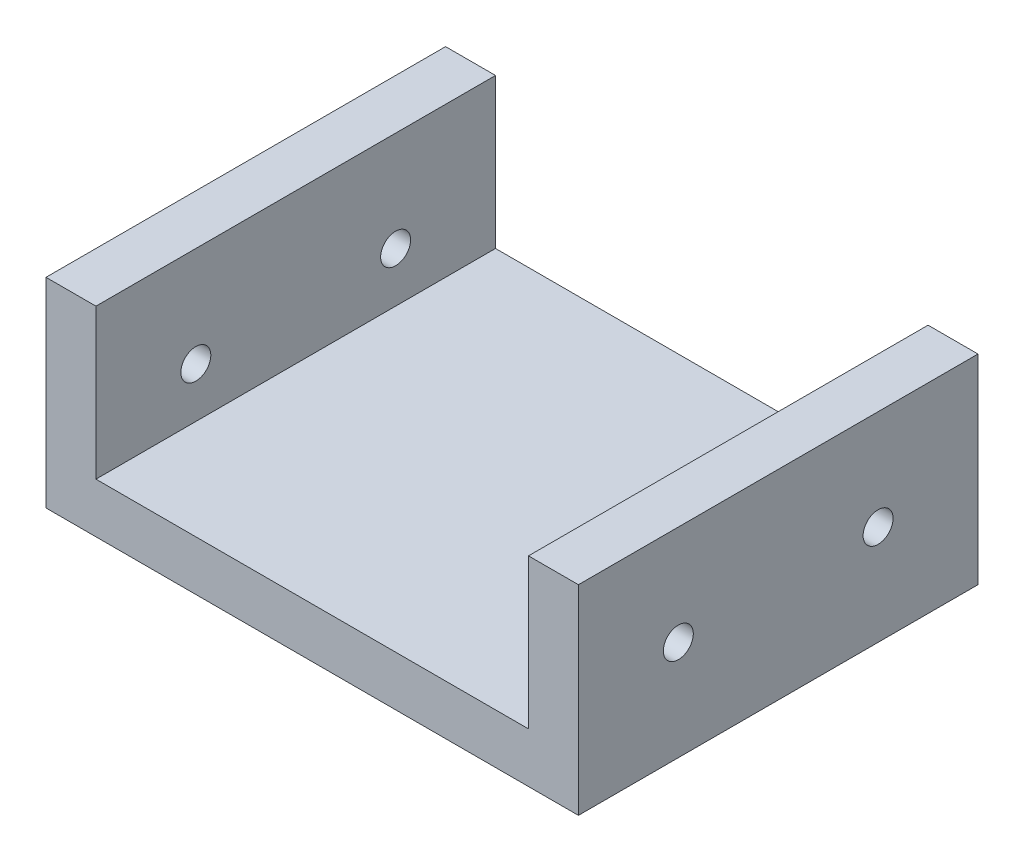
SolidWorks part; units mm, degrees
ref_plane "Plan de face" through (0, 0, 0) normal (0, 0, 1) x (1, 0, 0)
ref_plane "Plan de dessus" through (0, 0, 0) normal (0, 1, 0) x (1, 0, 0)
ref_plane "Plan de droite" through (0, 0, 0) normal (1, 0, 0) x (0, 0, -1)
sketch "Esquisse1" plane through (0, 0, 0) normal (0, 1, 0) x (1, 0, 0)
  line L1 (0, 0) -> (53.3, 0)
  line L2 (0, 0) -> (0, -40)
  line L3 (0, -40) -> (53.3, -40)
  line L4 (53.3, 0) -> (53.3, -40)
  dimension "D1" = 53.3
  dimension "D2" = 40
extrude "Boss.-Extru.1" add sketch "Esquisse1" along normal blind 20
sketch "Esquisse2" plane through (0, 20, 0) normal (0, 1, 0) x (1, 0, 0)
  line L0 (0, 0) -> (0, -40) construction
  line L1 (5, 0) -> (48.3, 0)
  line L2 (5, 0) -> (5, -40)
  line L3 (5, -40) -> (48.3, -40)
  line L4 (48.3, 0) -> (48.3, -40)
  line L5 (53.3, -40) -> (53.3, 0) construction
  line L6 (0, -40) -> (53.3, -40) construction
  line L7 (53.3, 0) -> (0, 0) construction
  dimension "D1" = 5
  dimension "D2" = 5
  dimension "D3" = 0
  dimension "D4" = 0
extrude "Enlèv. mat.-Extru.1" cut sketch "Esquisse2" against normal blind 15
sketch "Esquisse3" plane through (53.3, 0, 0) normal (1, 0, 0) x (0, 0, -1)
  line L0 (-40, 20) -> (-40, 0) construction
  line L1 (-40, 20) -> (0, 20) construction
  line L2 (-20, 20) -> (-20, 0) construction
  circle A0 centre (-30, 10) radius 1.5
  circle A1 centre (-10, 10) radius 1.5
  dimension "D3" = 3
  dimension "D1" = 10
  dimension "D2" = 10
extrude "Enlèv. mat.-Extru.2" cut sketch "Esquisse3" against normal through all
